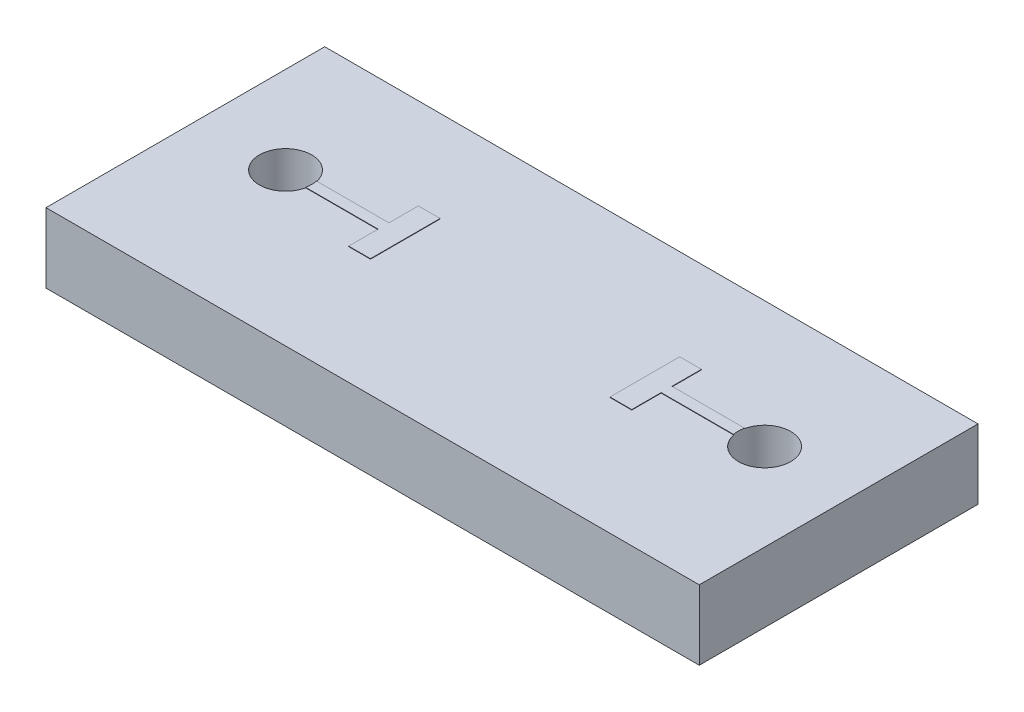
SolidWorks part; units mm, degrees
ref_plane "Front Plane" through (0, 0, 0) normal (0, 0, 1) x (1, 0, 0)
ref_plane "Top Plane" through (0, 0, 0) normal (0, 1, 0) x (1, 0, 0)
ref_plane "Right Plane" through (0, 0, 0) normal (1, 0, 0) x (0, 0, -1)
sketch "Sketch1" plane through (0, 0, 0) normal (0, 1, 0) x (1, 0, 0)
  line L1 (-7.5, -2) -> (7.5, -2)
  line L2 (-7.5, -2) -> (-7.5, 2)
  line L3 (-7.5, 2) -> (7.5, 2)
  line L4 (7.5, -2) -> (7.5, 2)
  line L5 (-7.5, -2) -> (7.5, 2) construction
  line L6 (-7.5, 2) -> (7.5, -2) construction
  point P0 (0, 0)
  dimension "D1" = 4
  dimension "D2" = 15
extrude "Boss-Extrude1" add sketch "Sketch1" along normal blind 1.6
sketch "Sketch2" plane through (0, 1.6, 0) normal (0, 1, 0) x (1, 0, 0)
  line L0 (0, -2) -> (0, 2) construction
  line L1 (-7.5, -2) -> (7.5, -2) construction
  line L2 (7.5, 2) -> (-7.5, 2) construction
  line L3 (-3.25, 0.8) -> (-2.75, 0.8)
  line L8 (0, 0) -> (3, 0)
  line L9 (-2.75, -0.8) -> (-2.75, 0.8)
  line L10 (3.25, -0.8) -> (2.75, -0.8)
  line L11 (3.25, -0.8) -> (3.25, 0.8)
  line L12 (3.25, 0.8) -> (2.75, 0.8)
  line L13 (2.75, -0.8) -> (2.75, 0.8)
  line L14 (3.25, -0.8) -> (2.75, 0.8) construction
  line L15 (3.25, 0.8) -> (2.75, -0.8) construction
  line L16 (-3.25, -0.8) -> (-2.75, -0.8)
  line L17 (-3.25, -0.8) -> (-3.25, 0.8)
  dimension "D3" = 3
  dimension "D4" = 0.5
  dimension "D5" = 1.6
sketch "Sketch3" plane through (0, 1.6, 0) normal (0, 1, 0) x (1, 0, 0)
  line L0 (0, -2) -> (0, 2) construction
  circle A0 centre (5.5, 0) radius 0.6
  circle A1 centre (-5.5, 0) radius 0.6
  dimension "D1" = 1.2
  dimension "D2" = 5.5
  dimension "D3" = 5.5
extrude "Cut-Extrude1" cut sketch "Sketch3" against normal blind 1.6 contours A0 | A1
extrude "Boss-Extrude2" add sketch "Sketch2" along normal blind 0.01
sketch "Sketch4" plane through (0, 1.6, 0) normal (0, 1, 0) x (1, 0, 0)
  line L0 (3.25, -0.8) -> (3.25, 0.8) construction
  line L1 (7.75, -0.125) -> (3.25, -0.125)
  line L2 (7.75, -0.125) -> (7.75, 0.125)
  line L3 (7.75, 0.125) -> (3.25, 0.125)
  line L4 (3.25, -0.125) -> (3.25, 0.125)
  line L5 (7.75, -0.125) -> (3.25, 0.125) construction
  line L6 (7.75, 0.125) -> (3.25, -0.125) construction
  line L7 (0, 0) -> (0, 2) construction
  line L8 (7.5, 2) -> (-7.5, 2) construction
  line L9 (-7.75, 0.125) -> (-3.25, 0.125)
  line L10 (-3.25, -0.125) -> (-3.25, 0.125)
  line L11 (-7.75, -0.125) -> (-3.25, -0.125)
  line L12 (-7.75, -0.125) -> (-7.75, 0.125)
  circle A0 centre (5.5, 0) radius 0.6
  circle A1 centre (-5.5, 0) radius 0.6
  point P0 (5.5, 0)
  line M8 (-3.25, -0.8) -> (-3.25, 0.8)
  line M14 (3.25, 0.8) -> (3.25, -0.8)
  circle M15 centre (5.5, 0) radius 0.6
  circle M16 centre (-5.5, 0) radius 0.6
  dimension "D2" = 1.2
  dimension "D1" = 0.25
extrude "Boss-Extrude3" add sketch "Sketch4" along normal blind 0.01 contours L3 L1 M15 M14 | L11 L9 M16 M8
sketch "Sketch5" plane through (0, 0, 2) normal (0, 0, 1) x (1, 0, 0)
  line L1 (-7.5, 1.6) -> (7.5, 1.6)
  line L2 (-7.5, 1.6) -> (-7.5, 0)
  line L3 (-7.5, 0) -> (7.5, 0)
  line L4 (7.5, 1.6) -> (7.5, 0)
extrude "Boss-Extrude4" add sketch "Sketch5" along normal blind 1.5
sketch "Sketch6" plane through (0, 0, -2) normal (0, 0, -1) x (-1, 0, 0)
  line L1 (7.5, 1.6) -> (-7.5, 1.6)
  line L2 (7.5, 1.6) -> (7.5, 0)
  line L3 (7.5, 0) -> (-7.5, 0)
  line L4 (-7.5, 1.6) -> (-7.5, 0)
extrude "Boss-Extrude5" add sketch "Sketch6" along normal blind 0.9
